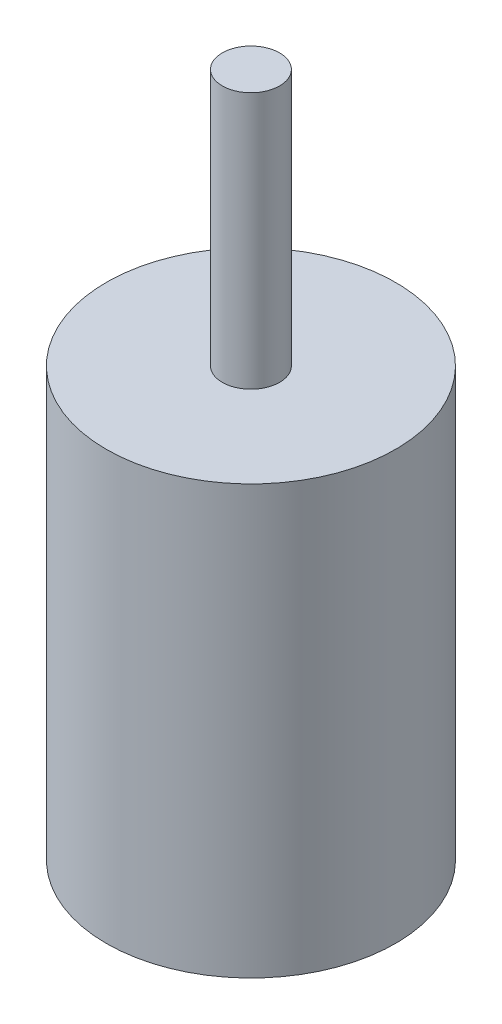
SolidWorks part; units mm, degrees
ref_plane "Front Plane" through (0, 0, 0) normal (0, 0, 1) x (1, 0, 0)
ref_plane "Top Plane" through (0, 0, 0) normal (0, 1, 0) x (1, 0, 0)
ref_plane "Right Plane" through (0, 0, 0) normal (1, 0, 0) x (0, 0, -1)
sketch "Sketch1" plane through (0, 0, 0) normal (0, 1, 0) x (1, 0, 0)
  circle A0 centre (0, 0) radius 21.463
  dimension "D1" = 42.926
extrude "Boss-Extrude1" add sketch "Sketch1" along normal blind 63.5
sketch "Sketch2" plane through (0, 63.5, 0) normal (0, 1, 0) x (1, 0, 0)
  circle A0 centre (0, 0) radius 4.25
  dimension "D1" = 8.5
extrude "Boss-Extrude2" add sketch "Sketch2" along normal blind 38.1
